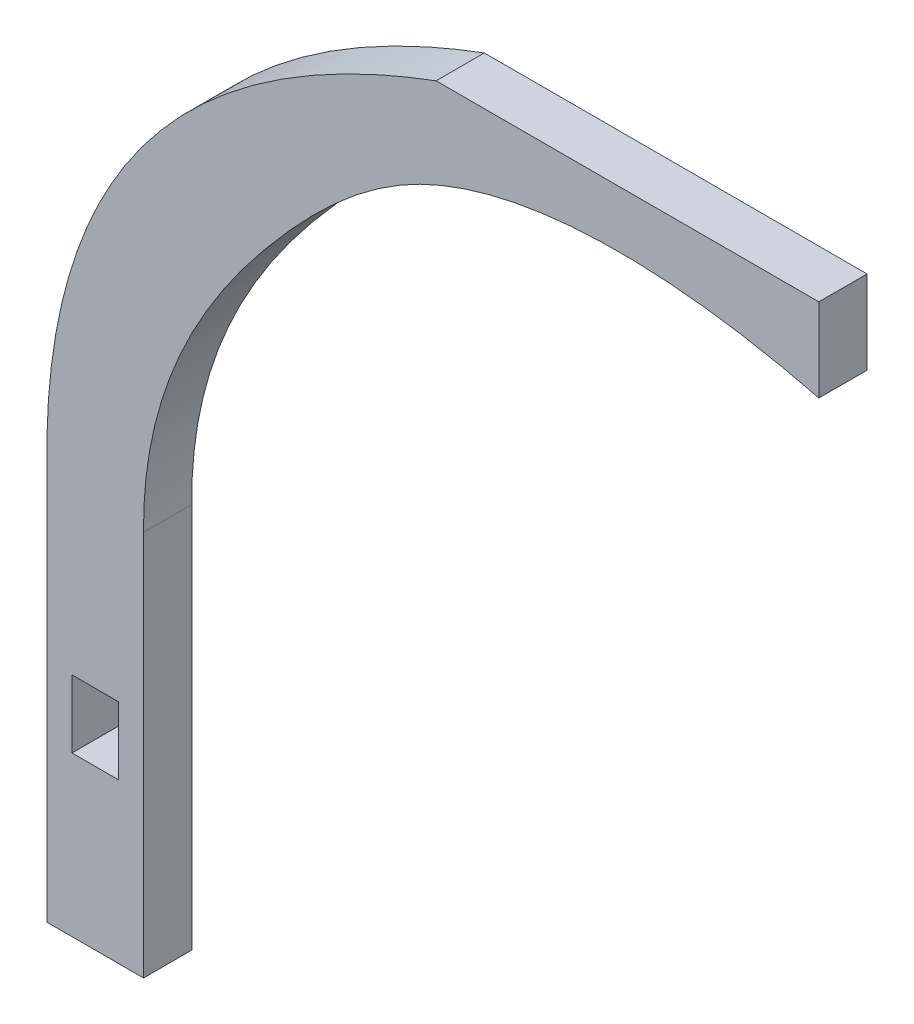
SolidWorks part; units mm, degrees
ref_plane "Plan de face" through (0, 0, 0) normal (0, 0, 1) x (1, 0, 0)
ref_plane "Plan de dessus" through (0, 0, 0) normal (0, 1, 0) x (1, 0, 0)
ref_plane "Plan de droite" through (0, 0, 0) normal (1, 0, 0) x (0, 0, -1)
sketch "Esquisse1" plane through (0, 0, 0) normal (0, 0, 1) x (1, 0, 0)
  line L0 (75, 75.6988) -> (-82.5094, 75.6988) construction
  line L1 (-2.413, -3.5052) -> (2.413, -3.5052)
  line L2 (-2.413, -3.5052) -> (-2.413, 3.5052)
  line L3 (-2.413, 3.5052) -> (2.413, 3.5052)
  line L4 (2.413, -3.5052) -> (2.413, 3.5052)
  line L5 (-2.413, -3.5052) -> (2.413, 3.5052) construction
  line L6 (-2.413, 3.5052) -> (2.413, -3.5052) construction
  line L7 (-5, 20) -> (5, 20)
  line L8 (-5, 20) -> (-5, -20)
  line L9 (-5, -20) -> (5, -20)
  line L10 (5, 20) -> (5, -20)
  line L11 (0, 0) -> (-111.4712, 0) construction
  line L12 (35.3257, 75.6988) -> (75, 75.6988)
  line L13 (75, 75.6988) -> (75, 67.0595)
  spline S0 degree 2 poles (-5, 20) (-6.0831, 60.3797) (35.3257, 75.6988) knots 0 0 0 1 1 1
  spline S1 degree 3 poles (75, 67.0595) (62.0309, 70.3669) (38.2696, 72.4069) (13.9373, 49.4176) (4.8755, 33.4479) (5, 20) knots 0 0 0 0 0.444261 0.615866 1 1 1 1
  point P0 (0, 0)
  dimension "D1" = 4.826
  dimension "D2" = 7.0104
  dimension "D3" = 10
  dimension "D4" = 5
  dimension "D5" = 20
  dimension "D6" = 40
  dimension "D7" = 70
extrude "Boss.-Extru.2" add sketch "Esquisse1" along normal blind 5
